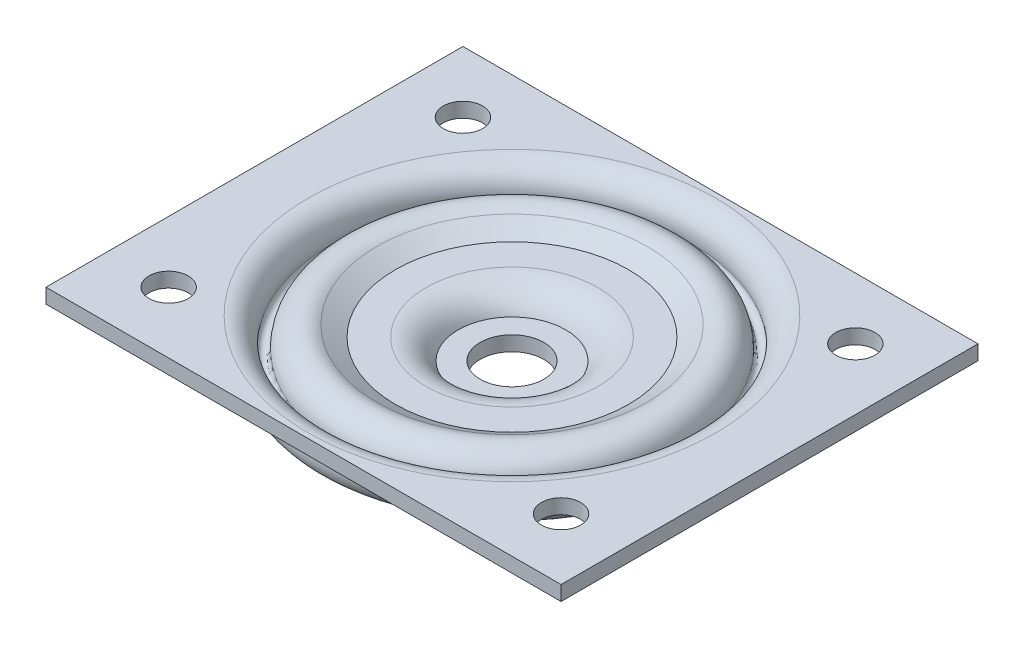
SolidWorks part; units mm, degrees
ref_plane "Front Plane" through (0, 0, 0) normal (0, 0, 1) x (1, 0, 0)
ref_plane "Top Plane" through (0, 0, 0) normal (0, 1, 0) x (1, 0, 0)
ref_plane "Right Plane" through (0, 0, 0) normal (1, 0, 0) x (0, 0, -1)
sketch "Sketch1" plane through (0, 0, 0) normal (0, 0, 1) x (1, 0, 0)
  line L0 (0, 0) -> (0, 25.5273) construction
  line L1 (6.5, 3) -> (6.5, 0)
  line L2 (6.5, 3) -> (10.9548, 3)
  line L3 (17.5, 7.2) -> (23.7791, 7.2)
  line L4 (23.7791, 7.2) -> (27.5481, 9.4296)
  line L5 (41.5, 11) -> (52.5, 11)
  line L6 (6.5, 0) -> (13.3, 0)
  line L7 (17.5, 4.2) -> (24.6, 4.2)
  line L8 (24.6, 4.2) -> (29.0756, 6.8475)
  line L9 (41.5, 8) -> (52.5, 8)
  line L10 (52.5, 11) -> (52.5, 8)
  arc A0 (10.9548, 3) -> (17.5, 7.2) centre (17.5, 0) cw
  arc A2 (27.5481, 9.4296) -> (34.8097, 5.0388) centre (30.0001, 5.2846) cw
  arc A3 (34.8097, 5.0388) -> (36.7871, 5.1935) centre (35.8084, 4.9878) ccw
  arc A4 (36.7871, 5.1935) -> (41.5, 11) centre (41.5, 6.1841) cw
  arc A5 (13.3, 0) -> (17.5, 4.2) centre (17.5, 0) cw
  arc A6 (29.0756, 6.8475) -> (31.8137, 5.1919) centre (30.0001, 5.2846) cw
  arc A7 (31.8137, 5.1919) -> (39.7229, 5.8106) centre (35.8084, 4.9878) ccw
  arc A8 (39.7229, 5.8106) -> (41.5, 8) centre (41.5, 6.1841) cw
  point P9 (36.1204, 1)
  dimension "D7" = 11
  dimension "D10" = 4
  dimension "D11" = 3
  dimension "D5" = 4.2
  dimension "D6" = 1
  dimension "D1" = 52.5
  dimension "D2" = 8
  dimension "D3" = 6.8
  dimension "D4" = 6.5
  dimension "D8" = 7.1
  dimension "D9" = 5.2
revolve "Revolve1" add sketch "Sketch1" angle 360 about L0
sketch "Sketch2" plane through (0, 11, 0) normal (0, 1, 0) x (1, 0, 0)
  line L1 (52.5, -42.5) -> (-52.5, -42.5)
  line L2 (52.5, -42.5) -> (52.5, 42.5)
  line L3 (52.5, 42.5) -> (-52.5, 42.5)
  line L4 (-52.5, -42.5) -> (-52.5, 42.5)
  line L5 (52.5, -42.5) -> (-52.5, 42.5) construction
  line L6 (52.5, 42.5) -> (-52.5, -42.5) construction
  circle A1 centre (0, 0) radius 52.5 construction
  point P0 (0, 0)
  dimension "D1" = 85
extrude "Cut-Extrude1" cut sketch "Sketch2" against normal blind 10 flip side to cut
sketch "Sketch4" plane through (0, 11, 0) normal (0, 1, 0) x (1, 0, 0)
  line L0 (-30.8221, 42.5) -> (-52.5, 42.5)
  line L1 (-52.5, 42.5) -> (-52.5, -42.5)
  line L2 (-52.5, -42.5) -> (-30.8221, -42.5)
  line L3 (30.8221, 42.5) -> (52.5, 42.5)
  line L4 (52.5, 42.5) -> (52.5, -42.5)
  line L5 (52.5, -42.5) -> (30.8221, -42.5)
  arc A0 (30.8221, -42.5) -> (30.8221, 42.5) centre (0, 0) ccw construction
  arc A1 (-30.8221, 42.5) -> (-30.8221, -42.5) centre (0, 0) ccw construction
  arc A2 (-30.8221, 42.5) -> (-30.8221, -42.5) centre (0, 0) ccw
  arc A3 (30.8221, -42.5) -> (30.8221, 42.5) centre (0, 0) ccw
  point P3 (-52.5, 0)
  arc M6 (30.8221, -42.5) -> (30.8221, 42.5) centre (0, 0) ccw
  arc M8 (-30.8221, 42.5) -> (-30.8221, -42.5) centre (0, 0) ccw
  dimension "D1" = 105
extrude "Boss-Extrude1" add sketch "Sketch4" against normal up to surface (3 mm away) contours L0 L1 M8 | L1 L2 M8 | L4 L3 M6 | L5 L4 M6 up to face at (0, 8, -41.5)
sketch "Sketch5" plane through (0, 11, 0) normal (0, 1, 0) x (1, 0, 0)
  line L1 (40, -30) -> (-40, -30) construction
  line L2 (40, -30) -> (40, 30) construction
  line L3 (40, 30) -> (-40, 30) construction
  line L4 (-40, -30) -> (-40, 30) construction
  line L5 (40, -30) -> (-40, 30) construction
  line L6 (40, 30) -> (-40, -30) construction
  circle A0 centre (-40, 30) radius 4
  circle A1 centre (40, 30) radius 4
  circle A2 centre (40, -30) radius 4
  circle A3 centre (-40, -30) radius 4
  point P0 (0, 0)
  dimension "D3" = 8
  dimension "D1" = 60
  dimension "D2" = 80
extrude "Cut-Extrude2" cut sketch "Sketch5" against normal through all
